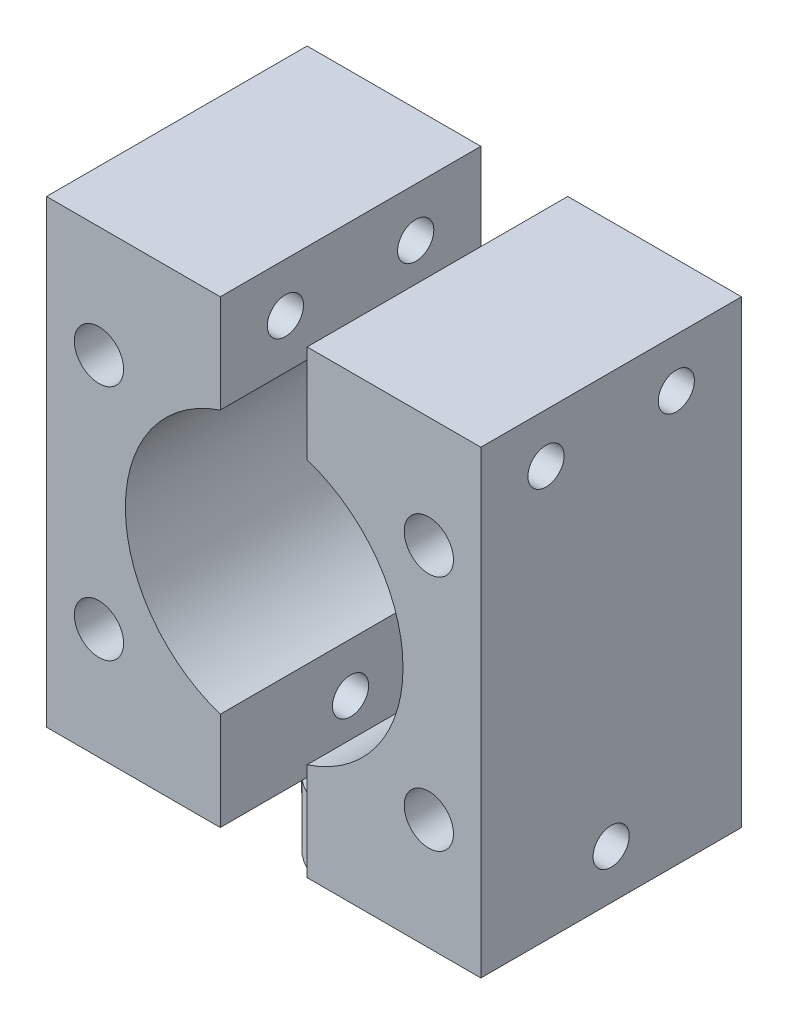
SolidWorks part; units mm, degrees
material "Plain Carbon Steel"
ref_plane "Front Plane" through (0, 0, 0) normal (0, 0, 1) x (1, 0, 0)
ref_plane "Top Plane" through (0, 0, 0) normal (0, 1, 0) x (1, 0, 0)
ref_plane "Right Plane" through (0, 0, 0) normal (1, 0, 0) x (0, 0, -1)
sketch "Sketch1" plane through (0, 0, 0) normal (0, 1, 0) x (1, 0, 0)
  line L0 (0, 4.75) -> (0, -4.75) construction
  line L1 (1.5, 4.5069) -> (1.5, -4.5069)
  line L2 (-1.5, 4.5069) -> (-1.5, -4.5069)
  circle A0 centre (0, 0) radius 4.75
  dimension "D1" = 9.5
  dimension "D2" = 1.5
ref_plane "GroundPlane" through (0, 4.5, 0) normal (0, 1, 0) x (-1, 0, 0)
sketch "Sketch2" plane through (0, 4.5, 0) normal (0, 1, 0) x (-1, 0, 0)
  line L0 (0, 7.5) -> (6.4952, -3.75) construction
  line L1 (0, 7.5) -> (0, -7.5) construction
  line L2 (0, 12.7) -> (0, -12.7) construction
  line L3 (0, 7.5) -> (-6.4952, -3.75) construction
  line L4 (-9.2393, -11.2686) -> (9.8107, -11.2686) construction
  line L5 (-9.2393, -11.2686) -> (-9.2393, -30.3186) construction
  line L6 (-9.2393, -30.3186) -> (9.8107, -30.3186) construction
  line L7 (9.8107, -11.2686) -> (9.8107, -30.3186) construction
  line L8 (-6.4952, -3.75) -> (6.4952, -3.75) construction
  line L9 (0, -7.5) -> (6.4952, 3.75) construction
  line L10 (6.4952, 3.75) -> (-6.4952, 3.75) construction
  line L11 (-6.4952, 3.75) -> (0, -7.5) construction
  line L12 (3, -8.6561) -> (3, 9.3439)
  line L13 (3, -8.6561) -> (15, -8.6561)
  line L14 (3, 9.3439) -> (15, 9.3439)
  line L15 (15, 9.3439) -> (15, -8.6561)
  line L16 (-3, -8.6561) -> (-3, 9.3439)
  line L17 (-3, -8.6561) -> (-15, -8.6561)
  line L18 (-3, 9.3439) -> (-15, 9.3439)
  line L19 (-15, 9.3439) -> (-15, -8.6561)
  circle A0 centre (0, 0) radius 7.5 construction
  dimension "D1" = 15
  dimension "D2" = 30
  dimension "D3" = 25.4
  dimension "D4" = 19.05
  dimension "D5" = 19.05
  dimension "D6" = 30
  dimension "D7" = 30
  dimension "D8" = 3
  dimension "D9" = 18
  dimension "D10" = 12
ref_plane "TopPlane" through (0, 36.25, 0) normal (0, 1, 0) x (-1, 0, 0)
extrude "Extrude1" add sketch "Sketch2" along normal blind 31.75
extrude "Extrude2" add sketch "Sketch1" along normal blind 4.5 contours L1 A0 | L2 A0
sketch "Sketch4" plane through (0, 0, 9.3439) normal (0, 0, 1) x (1, 0, 0)
  line L0 (-14.9586, 36.25) -> (15.0262, 4.5) construction
  line L1 (9.9, 36.25) -> (-9.9, 36.25) construction
  line L2 (9.9, 4.5) -> (-9.9, 4.5) construction
  line L3 (15.0262, 36.25) -> (-14.9586, 4.5) construction
  circle A0 centre (0.0338, 20.375) radius 9.5885
  point P8 (0.0338, 20.375)
  dimension "D1" = 19.177
extrude "Extrude3" cut sketch "Sketch4" against normal blind 17
sketch "Sketch6" plane through (15, 0, 0) normal (1, 0, 0) x (0, 0, -1)
  line L0 (-9.3439, 36.25) -> (-9.3439, 4.5) construction
  line L1 (-9.3439, 20.375) -> (8.6561, 20.375) construction
  line L2 (8.6561, 36.25) -> (8.6561, 4.5) construction
  line L3 (-0.3439, 36.25) -> (-0.3439, 4.5) construction
  line L4 (-9.3439, 36.25) -> (8.6561, 36.25) construction
  line L5 (-9.3439, 4.5) -> (8.6561, 4.5) construction
  line L6 (-0.3439, 36.25) -> (-9.3439, 29.4932) construction
  point P12 (-4.8439, 32.8716)
  point P15 (4.1561, 32.8716)
  point P16 (4.1561, 7.8784)
  point P17 (-4.8439, 7.8784)
  point P18 (-0.3439, 32.8716)
  point P19 (-0.3439, 7.8784)
sketch "Sketch9" plane through (0, 0, 9.3439) normal (0, 0, 1) x (1, 0, 0)
  line L0 (-15, 31.1716) -> (-7.7544, 25.9681) construction
  line L1 (-15, 9.5784) -> (-7.7544, 14.7819) construction
  line L2 (15, 9.5784) -> (7.81, 14.7652) construction
  line L3 (15, 36.25) -> (15, 4.5) construction
  line L4 (15, 31.1716) -> (7.81, 25.9848) construction
  line L5 (15, 36.25) -> (15, 29.4932) construction
  line L6 (-15, 31.1716) -> (15, 31.1716) construction
  line L7 (16.5, 36.25) -> (-16.5, 36.25) construction
  arc A0 (-3, 29.4709) -> (-3, 11.2791) centre (0.0338, 20.375) ccw construction
  arc A1 (3, 11.2568) -> (3, 29.4932) centre (0.0338, 20.375) ccw construction
  point P20 (-11.3772, 28.5699)
  point P21 (-11.3772, 12.1801)
  point P22 (11.405, 12.1718)
  point P23 (11.405, 28.5782)
  dimension "D1" = 5.0784
hole_wizard "M3 Clearance Hole1" positions "3DSketch2" profile "Sketch11" hole size "M3" standard "Ansi Metric" end condition through all
sketch3d "3DSketch2"
  point P0 (-11.3772, 28.5699, 9.3439)
  point P3 (-11.3772, 12.1801, 9.3439)
  point P6 (11.405, 12.1718, 9.3439)
  point P9 (11.405, 28.5782, 9.3439)
sketch "Sketch11" plane through (-11.3772, 28.5699, 9.3439) normal (1, 0, 0) x (0, -1, 0)
  line L0 (0, 0) -> (0, 18)
  line L1 (0, 18) -> (1.7, 18)
  line L2 (1.7, 18) -> (1.7, 0)
  line L5 (1.7, 0) -> (0, 0)
  line L11 (0, -6.35) -> (0, 107.95) construction
  dimension "Thru Hole Dia." = 3.4
  dimension "Thru Hole Depth" = 18
sketch "Sketch14" plane through (0, 4.5, 0) normal (0, 1, 0) x (-1, 0, 0)
  point P0 (6.4952, 3.75)
  point P1 (-6.4952, 3.75)
  point P3 (0, -7.5)
sketch "Sketch16" plane through (0, 4.5, 0) normal (0, 1, 0) x (-1, 0, 0)
  point P0 (6.4952, 3.75)
  point P1 (-6.4952, 3.75)
  point P3 (0, -7.5)
hole_wizard "M3x0.5 Tapped Hole1" positions "3DSketch3" profile "Sketch18" tap size "M3x0.5" standard "Ansi Metric" end condition through all
sketch3d "3DSketch3"
  point P0 (15, 32.8716, 4.8439)
  point P3 (15, 32.8716, -4.1561)
  point P6 (15, 7.8784, 0.3439)
sketch "Sketch18" plane through (15, 32.8716, 4.8439) normal (0, 1, 0) x (0, 0, -1)
  line L0 (0, 0) -> (0, 30)
  line L1 (0, 30) -> (1.25, 30)
  line L2 (1.25, 30) -> (1.25, 0)
  line L5 (1.25, 0) -> (0, 0)
  line L11 (0, -6.35) -> (0, 107.95) construction
  dimension "Thru Tap Drill Dia." = 2.5
  dimension "Thru Tap Drill Depth" = 30
cosmetic thread "Hole Thread6" parameters "D2"=3
cosmetic thread "Hole Thread7" parameters "D2"=3
cosmetic thread "Hole Thread8" parameters "D2"=3
hole_wizard "M2x0.4 Tapped Hole2" positions "3DSketch8" profile "Sketch23" tap size "M2x0.4" standard "Ansi Metric"
sketch3d "3DSketch8"
  point P9 (-6.4952, 4.5, 3.75)
  point P11 (6.4952, 4.5, 3.75)
sketch "Sketch23" plane through (-6.4952, 4.5, 3.75) normal (1, 0, 0) x (0, 0, -1)
  line L0 (0, 0) -> (0, 6.4807)
  line L1 (0, 6.4807) -> (0.8, 6)
  line L2 (0.8, 6) -> (0.8, 0)
  line L5 (0.8, 0) -> (0, 0)
  line L10 (0, 6.4807) -> (-0.8, 6) construction
  line L11 (0, -6.35) -> (0, 107.95) construction
  dimension "Tap Drill Dia." = 1.6
  dimension "Tap Drill Depth" = 6
  dimension "Drill Angle" = 118
cosmetic thread "Hole Thread16" parameters "D1"=4, "D2"=2
cosmetic thread "Hole Thread17" parameters "D1"=4, "D2"=2
